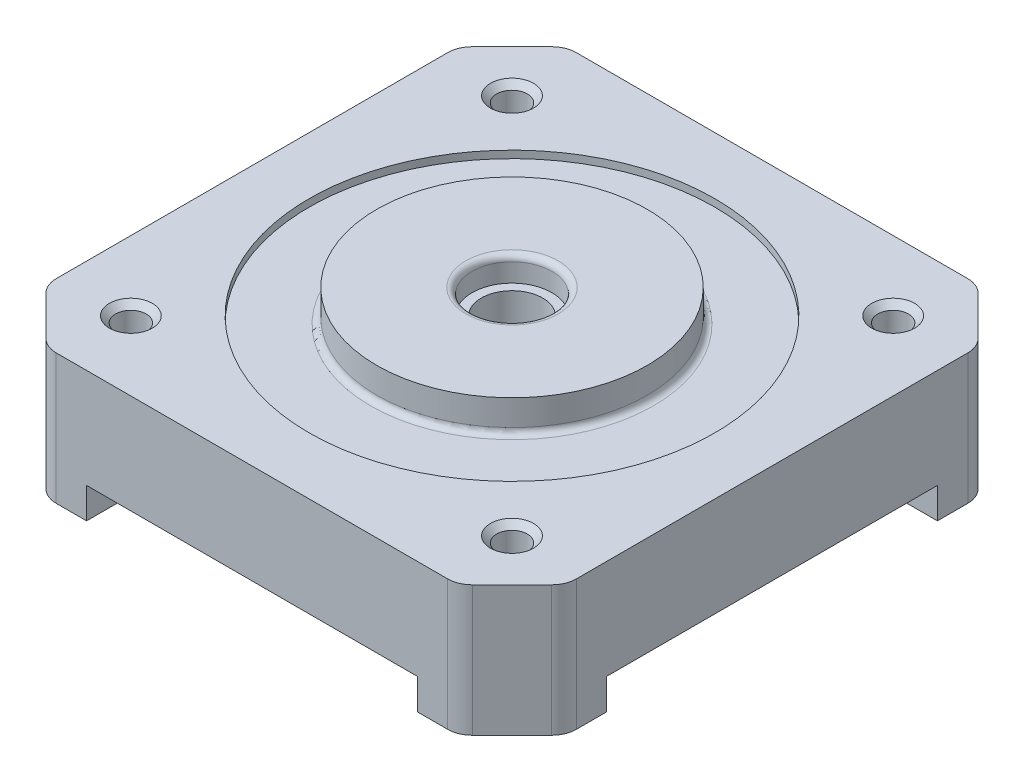
SolidWorks part; units mm, degrees
material "Alumina"
ref_plane "Front Plane" through (0, 0, 0) normal (0, 0, 1) x (1, 0, 0)
ref_plane "Top Plane" through (0, 0, 0) normal (0, 1, 0) x (1, 0, 0)
ref_plane "Right Plane" through (0, 0, 0) normal (1, 0, 0) x (0, 0, -1)
sketch "Sketch1" plane through (0, 0, 0) normal (0, 1, 0) x (1, 0, 0)
  line L0 (-21.15, 16.7509) -> (-16.7509, 21.15)
  line L1 (-16.7509, -21.15) -> (16.7509, -21.15)
  line L2 (-21.15, -16.7509) -> (-21.15, 16.7509)
  line L3 (-16.7509, 21.15) -> (16.7509, 21.15)
  line L4 (21.15, -16.7509) -> (21.15, 16.7509)
  line L7 (16.7509, 21.15) -> (21.15, 16.7509)
  line L8 (16.7509, -21.15) -> (21.15, -16.7509)
  line L9 (-21.15, -16.7509) -> (-16.7509, -21.15)
  point P0 (0, 0)
  dimension "D1" = 42.3
  dimension "D2" = 42.3
  dimension "D3" = 53.6
  dimension "D4" = 45
  dimension "D5" = 45
  dimension "D7" = 53.6
extrude "Boss-Extrude1" add sketch "Sketch1" along normal blind 10.6
sketch "Sketch2" plane through (0, 10.6, 0) normal (0, 1, 0) x (1, 0, 0)
  circle A0 centre (0, 0) radius 16.5
  dimension "D1" = 33
extrude "Cut-Extrude1" cut sketch "Sketch2" against normal blind 0.6
sketch "Sketch3" plane through (0, 10, 0) normal (0, 1, 0) x (1, 0, 0)
  circle A0 centre (0, 0) radius 11
  dimension "D1" = 22
extrude "Boss-Extrude2" add sketch "Sketch3" along normal blind 2.6
sketch "Sketch4" plane through (0, 12.6, 0) normal (0, 1, 0) x (1, 0, 0)
  circle A0 centre (0, 0) radius 3.25
  dimension "D1" = 6.5
extrude "Cut-Extrude2" cut sketch "Sketch4" against normal blind 2
sketch "Sketch5" plane through (0, 10.6, 0) normal (0, 1, 0) x (1, 0, 0)
  circle A0 centre (0, 0) radius 2.5
  dimension "D1" = 5
extrude "Cut-Extrude3" cut sketch "Sketch5" against normal through all
fillet "Fillet1" radius 0.5 1 edges at (0, 12.6, 3.25)
fillet "Fillet2" radius 0.5 1 edges at (0, 10, 11)
hole_wizard "M3x0.5 Tapped Hole1" positions "Sketch9" profile "Sketch8" tap size "M3x0.5" standard "ANSI Metric"
sketch "Sketch9" plane through (0, 10.6, 0) normal (0, 1, 0) x (1, 0, 0)
  point P0 (-15.5, 15.5)
  point P2 (15.5, 15.5)
  point P4 (15.5, -15.5)
  point P6 (-15.5, -15.5)
  dimension "D1" = 31
  dimension "D2" = 31
  dimension "D3" = 31
  dimension "D4" = 31
  dimension "D5" = 5.65
  dimension "D6" = 5.65
  dimension "D7" = 5.65
  dimension "D8" = 5.65
sketch "Sketch8" plane through (-15.5, 10.6, -15.5) normal (1, 0, 0) x (0, 0, 1)
  line L0 (0, 0) -> (0, 10.7511)
  line L1 (0, 10.7511) -> (1.25, 10)
  line L2 (1.25, 10) -> (1.25, 0.5)
  line L3 (1.25, 0.5) -> (1.75, 0)
  line L5 (1.75, 0) -> (0, 0)
  line L6 (-1.25, 0.5) -> (-1.75, 0) construction
  line L10 (0, 10.7511) -> (-1.25, 10) construction
  line L11 (0, -6.35) -> (0, 107.95) construction
  dimension "Tap Drill Dia." = 2.5
  dimension "Tap Drill Depth" = 10
  dimension "Near C'Sink Dia." = 3.5
  dimension "Near C'Sink Angle" = 90
  dimension "Drill Angle" = 118
sketch "Sketch10" plane through (0, 0, 21.15) normal (0, 0, 1) x (1, 0, 0)
  line L0 (-13.4509, 0) -> (-13.4509, 2.5)
  line L1 (-16.7509, 0) -> (16.7509, 0) construction
  line L2 (-13.4509, 2.5) -> (13.4509, 2.5)
  line L3 (13.4509, 2.5) -> (13.4509, 0)
  line L4 (-16.7509, 10.6) -> (-16.7509, 0) construction
  line L5 (16.7509, 10.6) -> (16.7509, 0) construction
  line L6 (-13.4509, 0) -> (13.4509, 0)
  dimension "D1" = 3.3
  dimension "D2" = 3.3
  dimension "D3" = 2.5
extrude "Cut-Extrude4" cut sketch "Sketch10" against normal through all
sketch "Sketch11" plane through (-21.15, 0, 0) normal (-1, 0, 0) x (0, 0, 1)
  line L0 (-13.4509, 0) -> (-13.4509, 2.5)
  line L1 (-16.7509, 0) -> (16.7509, 0) construction
  line L2 (-13.4509, 2.5) -> (13.4509, 2.5)
  line L3 (13.4509, 2.5) -> (13.4509, 0)
  line L4 (13.4509, 0) -> (-13.4509, 0)
  line L5 (-16.7509, 10.6) -> (-16.7509, 0) construction
  line L6 (16.7509, 10.6) -> (16.7509, 0) construction
  dimension "D1" = 2.5
  dimension "D2" = 3.3
  dimension "D3" = 3.3
extrude "Cut-Extrude5" cut sketch "Sketch11" against normal through all
fillet "Fillet3" radius 2 8 edges at (-21.15, 5.3, 16.7509) (16.7509, 5.3, -21.15) (21.15, 5.3, -16.7509) (21.15, 5.3, 16.7509) (16.7509, 5.3, 21.15) (-16.7509, 5.3, 21.15) (-16.7509, 5.3, -21.15) (-21.15, 5.3, -16.7509)
